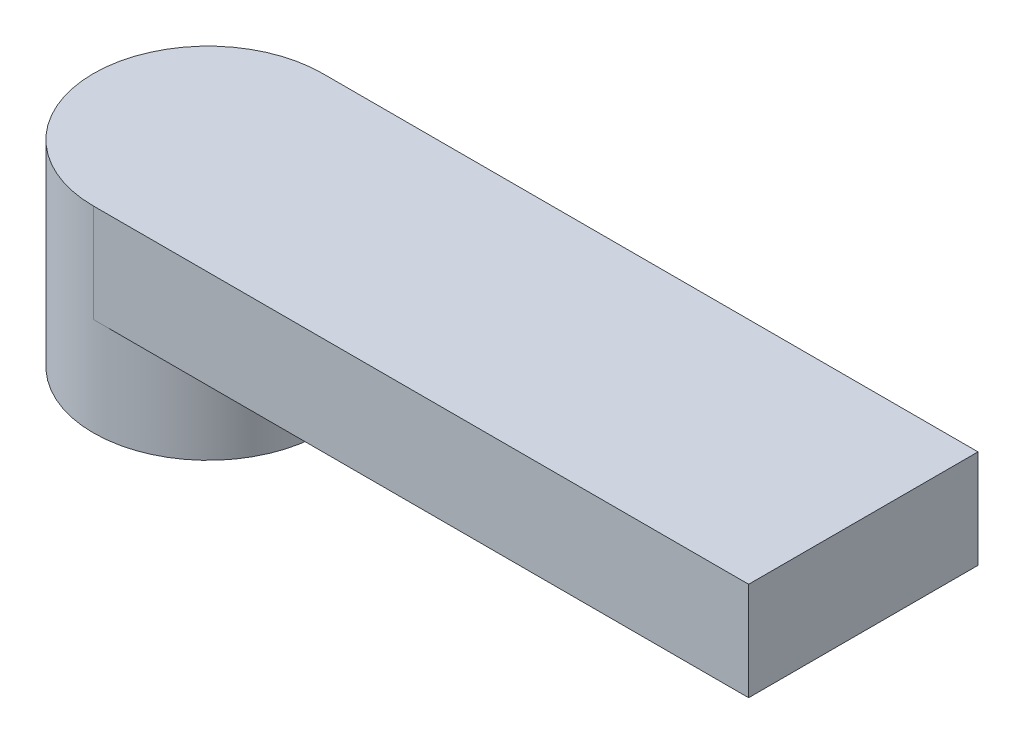
SolidWorks part; units mm, degrees
ref_plane "Front Plane" through (0, 0, 0) normal (0, 0, 1) x (1, 0, 0)
ref_plane "Top Plane" through (0, 0, 0) normal (0, 1, 0) x (1, 0, 0)
ref_plane "Right Plane" through (0, 0, 0) normal (1, 0, 0) x (0, 0, -1)
sketch "Sketch2" plane through (0, 0, 0) normal (0, 1, 0) x (1, 0, 0)
  circle A1 centre (0, 0) radius 3.5
  dimension "D1" = 7
extrude "Boss-Extrude1" add sketch "Sketch2" along normal blind 6
sketch "Sketch3" plane through (0, 0, 0) normal (0, -1, 0) x (1, 0, 0)
  circle A0 centre (0, 0) radius 2.475
  dimension "D1" = 4.95
extrude "Cut-Extrude1" cut sketch "Sketch3" against normal blind 2.5
sketch "Sketch4" plane through (0, 6, 0) normal (0, 1, 0) x (1, 0, 0)
  line L0 (0, 3.5) -> (20, 3.5)
  line L1 (20, 3.5) -> (20, -3.5)
  line L2 (20, -3.5) -> (0, -3.5)
  circle A0 centre (0, 0) radius 3.5 construction
  arc A1 (0, -3.5) -> (0, 3.5) centre (0, 0) ccw
  dimension "D1" = 20
extrude "Boss-Extrude2" add sketch "Sketch4" against normal blind 3
